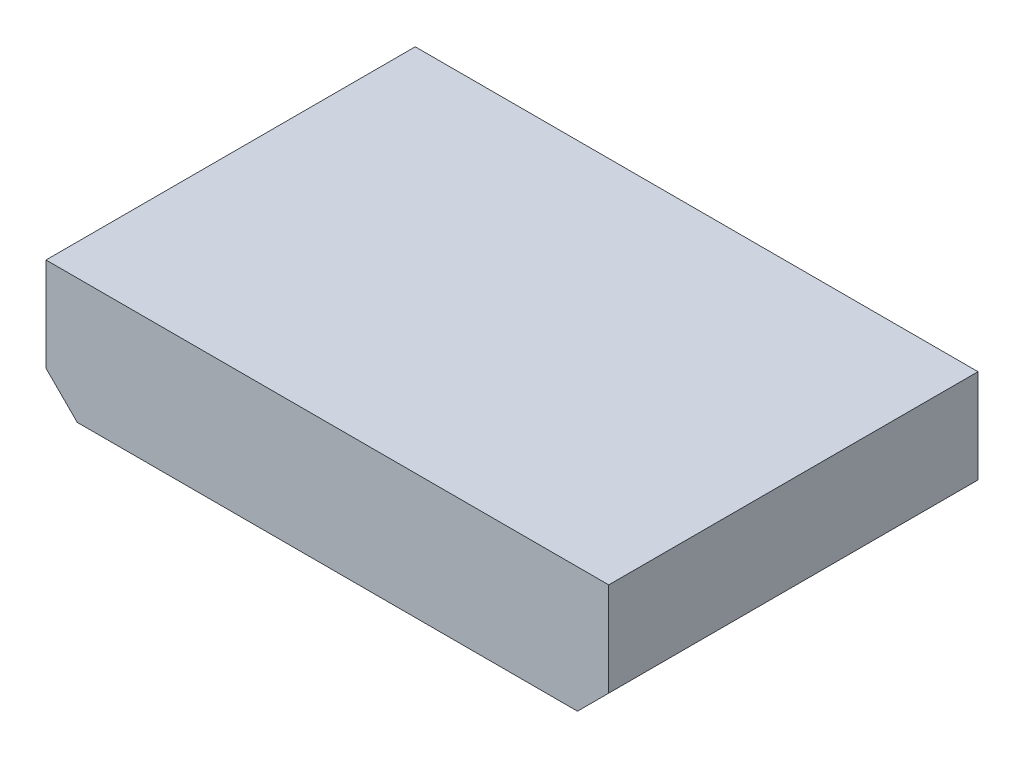
SolidWorks part; units mm, degrees
ref_plane "Front Plane" through (0, 0, 0) normal (0, 0, 1) x (1, 0, 0)
ref_plane "Top Plane" through (0, 0, 0) normal (0, 1, 0) x (1, 0, 0)
ref_plane "Right Plane" through (0, 0, 0) normal (1, 0, 0) x (0, 0, -1)
sketch "Sketch1" plane through (0, 0, 0) normal (0, 0, 1) x (1, 0, 0)
  line L0 (-5.08, 2.54) -> (-5.08, -1.27)
  line L1 (-5.08, -1.27) -> (-3.81, -2.54)
  line L2 (-3.81, -2.54) -> (16.51, -2.54)
  line L3 (16.51, -2.54) -> (17.78, -1.27)
  line L4 (17.78, -1.27) -> (17.78, 2.54)
  line L5 (17.78, 2.54) -> (-5.08, 2.54)
extrude "Component_Outline" add sketch "Sketch1" along normal blind 15 separate body
sketch "Sketch2" plane through (0, 0, 0) normal (0, 0, 1) x (1, 0, 0)
  circle A0 centre (0, 0) radius 0.25
extrude "1" add sketch "Sketch2" against normal blind 2 separate body
sketch "Sketch3" plane through (0, 0, 0) normal (0, 0, 1) x (1, 0, 0)
  circle A0 centre (2.54, 0) radius 0.25
extrude "2" add sketch "Sketch3" against normal blind 2 separate body
sketch "Sketch4" plane through (0, 0, 0) normal (0, 0, 1) x (1, 0, 0)
  circle A0 centre (5.08, 0) radius 0.25
extrude "3" add sketch "Sketch4" against normal blind 2 separate body
sketch "Sketch5" plane through (0, 0, 0) normal (0, 0, 1) x (1, 0, 0)
  circle A0 centre (7.62, 0) radius 0.25
extrude "4" add sketch "Sketch5" against normal blind 2 separate body
sketch "Sketch6" plane through (0, 0, 0) normal (0, 0, 1) x (1, 0, 0)
  circle A0 centre (10.16, 0) radius 0.25
extrude "5" add sketch "Sketch6" against normal blind 2 separate body
sketch "Sketch7" plane through (0, 0, 0) normal (0, 0, 1) x (1, 0, 0)
  circle A0 centre (12.7, 0) radius 0.25
extrude "6" add sketch "Sketch7" against normal blind 2 separate body
sketch3d "3DSketch1"
  line L0 (0, 0, 0) -> (1, 0, 0)
  line L1 (0, 0, 0) -> (0, 1, 0)
  line L2 (0, 0, 0) -> (0, 0, 1)
  point P0 (0, 0, 0)
